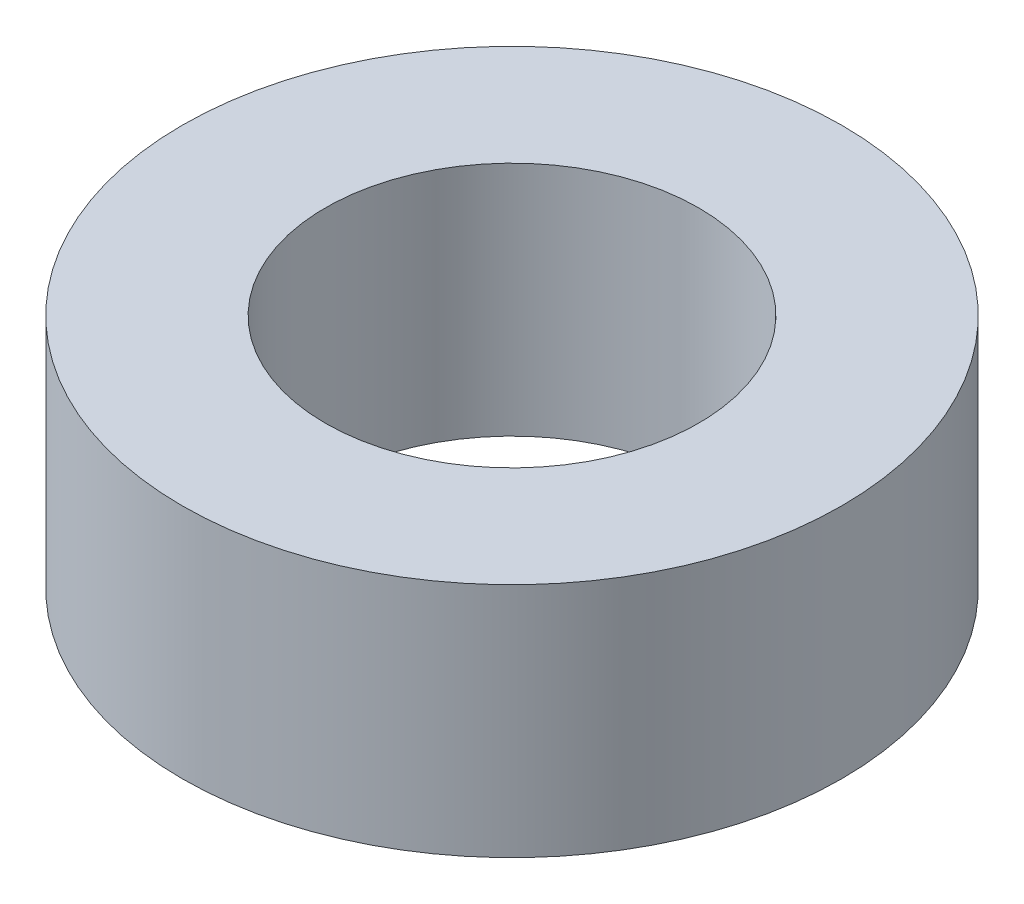
SolidWorks part; units mm, degrees
ref_plane "Front Plane" through (0, 0, 0) normal (0, 0, 1) x (1, 0, 0)
ref_plane "Top Plane" through (0, 0, 0) normal (0, 1, 0) x (1, 0, 0)
ref_plane "Right Plane" through (0, 0, 0) normal (1, 0, 0) x (0, 0, -1)
sketch "Sketch1" plane through (0, 0, 0) normal (0, 1, 0) x (1, 0, 0)
  circle A0 centre (0, 0) radius 3
  circle A1 centre (0, 0) radius 5.3
  dimension "D1" = 6
  dimension "D2" = 10.6
extrude "Boss-Extrude1" add sketch "Sketch1" along normal blind 3.8
